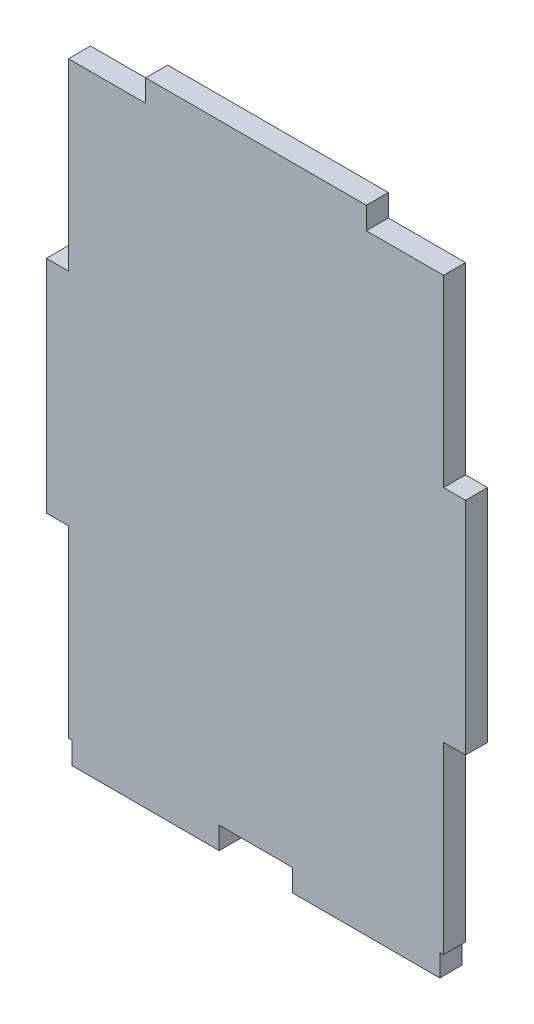
SolidWorks part; units mm, degrees
ref_plane "Front Plane" through (0, 0, 0) normal (0, 0, 1) x (1, 0, 0)
ref_plane "Top Plane" through (0, 0, 0) normal (0, 1, 0) x (1, 0, 0)
ref_plane "Right Plane" through (0, 0, 0) normal (1, 0, 0) x (0, 0, -1)
sketch "Sketch1" plane through (0, 0, 0) normal (0, 0, 1) x (1, 0, 0)
  line L0 (15, 40) -> (25.5, 40)
  line L1 (-25.5, -40) -> (-25, -40)
  line L2 (-25.5, -40) -> (-25.5, -15)
  line L3 (-25.5, 40) -> (-15, 40)
  line L4 (25.5, -40) -> (25.5, -15)
  line L5 (-25.5, -40) -> (25.5, 40) construction
  line L6 (-25.5, 40) -> (25.5, -40) construction
  line L7 (25.5, 15) -> (25.5, 40)
  line L8 (-15, 40) -> (-15, 43)
  line L9 (-15, 43) -> (15, 43)
  line L10 (15, 40) -> (15, 43)
  line L12 (-25, -40) -> (-25, -43)
  line L13 (-25, -43) -> (-5, -43)
  line L14 (-5, -40) -> (-5, -43)
  line L15 (-5, -40) -> (5, -40)
  line L16 (5, -40) -> (5, -43)
  line L17 (5, -43) -> (25, -43)
  line L18 (25, -40) -> (25, -43)
  line L19 (25.5, 15) -> (28.5, 15)
  line L20 (-25.5, 15) -> (-25.5, 40)
  line L21 (25.5, -15) -> (28.5, -15)
  line L22 (28.5, 15) -> (28.5, -15)
  line L23 (-25.5, 15) -> (-28.5, 15)
  line L24 (25, -40) -> (25.5, -40)
  line L25 (-25.5, -15) -> (-28.5, -15)
  line L26 (-28.5, 15) -> (-28.5, -15)
  point P0 (0, 0)
  dimension "D1" = 80
  dimension "D2" = 51
  dimension "D3" = 30
  dimension "D4" = 30
  dimension "D5" = 3
  dimension "D6" = 25
  dimension "D7" = 25
  dimension "D8" = 3
  dimension "D9" = 20
  dimension "D10" = 20
  dimension "D11" = 0.5
  dimension "D12" = 0.5
  dimension "D13" = 3
  dimension "D14" = 3
  dimension "D15" = 3
  dimension "D16" = 30
  dimension "D17" = 10.5
extrude "Boss-Extrude1" add sketch "Sketch1" along normal mid plane 3
